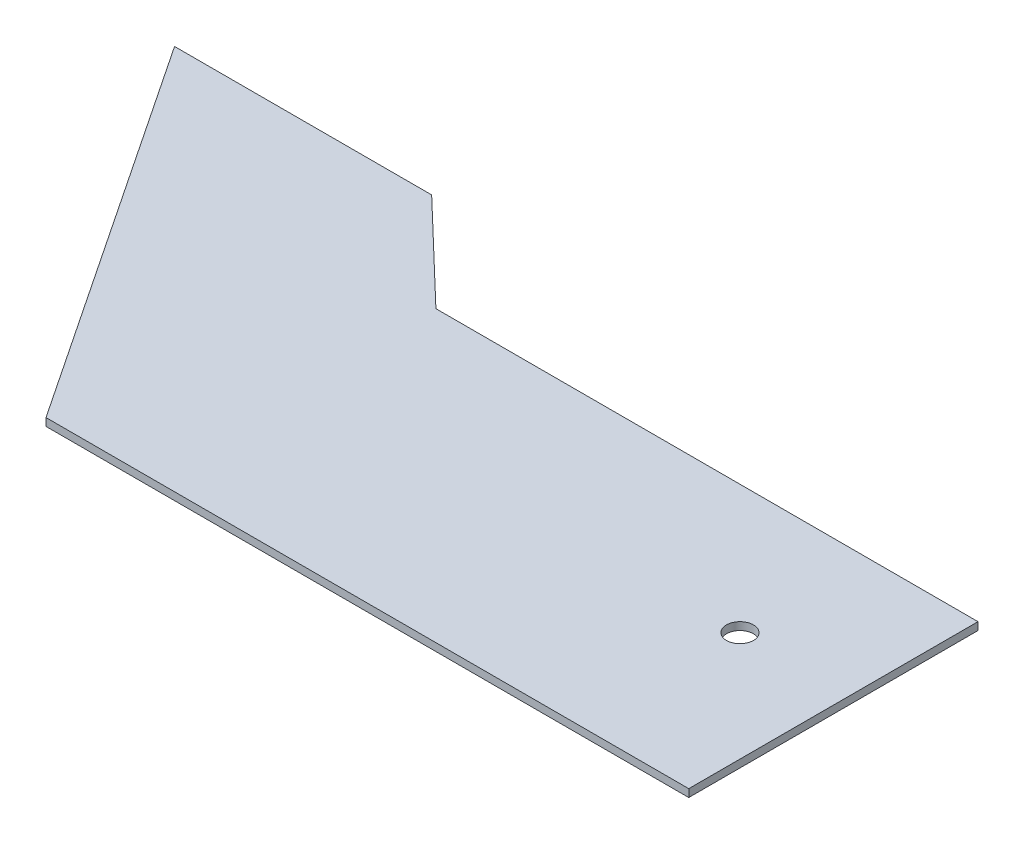
SolidWorks part; units mm, degrees
ref_plane "Front Plane" through (0, 0, 0) normal (0, 0, 1) x (1, 0, 0)
ref_plane "Top Plane" through (0, 0, 0) normal (0, 1, 0) x (1, 0, 0)
ref_plane "Right Plane" through (0, 0, 0) normal (1, 0, 0) x (0, 0, -1)
sketch "Sketch1" plane through (0, 0, 0) normal (0, 1, 0) x (1, 0, 0)
  line L0 (22.3813, 25.641) -> (56.4442, 25.6396) construction
  line L1 (-80.5873, 50.6403) -> (-45.5873, 0.6403)
  line L2 (-45.5873, 0.6403) -> (124.4127, 0.6403)
  line L4 (-80.5873, 50.6403) -> (159.4127, 50.6403)
  line L6 (-50.0418, 7.0039) -> (159.4127, 50.6403) construction
  line L7 (-80.5873, 50.6403) -> (128.8673, 7.0039) construction
  line L8 (159.4127, 50.6403) -> (124.4127, 0.6403)
  circle A0 centre (22.3813, 25.641) radius 2.1
  circle A1 centre (56.4442, 25.6396) radius 2.1
  point P4 (39.4127, 25.6403)
  dimension "D1" = 240
sketch "Sketch2" plane through (0, 0, 0) normal (0, 1, 0) x (1, 0, 0)
  line L0 (39.4127, 50.6403) -> (39.4127, 0.6403)
  line L1 (-80.5873, 50.6403) -> (159.4127, 50.6403) construction
  line L2 (-45.5873, 0.6403) -> (124.4127, 0.6403) construction
  line L3 (39.4127, 0.6403) -> (-45.5873, 0.6403)
  line L4 (-45.5873, 0.6403) -> (-80.5873, 50.6403)
  line L5 (-80.5873, 50.6403) -> (39.4127, 50.6403)
  circle A0 centre (22.3813, 25.641) radius 2.1
extrude "Boss-Extrude1" add sketch "Sketch2" along normal blind 1.2
sketch "Sketch3" plane through (0, 1.2, 0) normal (0, 1, 0) x (1, 0, 0)
  line L0 (39.4127, 40.6403) -> (-30.5873, 40.6403)
  line L1 (39.4127, 0.6403) -> (39.4127, 50.6403) construction
  line L2 (-30.5873, 40.6403) -> (-50.5873, 50.6403)
  line L3 (39.4127, 50.6403) -> (-80.5873, 50.6403) construction
  line L4 (-50.5873, 50.6403) -> (39.4127, 50.6403)
  line L5 (39.4127, 50.6403) -> (39.4127, 40.6403)
  dimension "D1" = 70
  dimension "D2" = 10
  dimension "D3" = 90
extrude "Cut-Extrude1" cut sketch "Sketch3" against normal blind 1.5
sketch "Sketch4" plane through (0, 1.2, 0) normal (0, 1, 0) x (1, 0, 0)
  line L1 (39.4127, 0.6403) -> (-60.5873, 0.6403)
  line L2 (39.4127, 0.6403) -> (39.4127, 45.6403)
  line L3 (-60.5873, 60.6403) -> (-100.5873, 60.6403)
  line L5 (39.4127, 45.6403) -> (-44.9268, 45.6403)
  line L6 (-44.9268, 45.6403) -> (-60.5873, 60.6403)
  line L7 (-100.5873, 60.6403) -> (-60.5873, 0.6403)
  circle A0 centre (22.3813, 25.641) radius 2.1
  dimension "D2" = 40
  dimension "D3" = 15
extrude "Boss-Extrude3" add sketch "Sketch4" against normal up to surface (1.2 mm away) contours L2 L5 L6 L3 L7 L1 | A0 up to face at (-21.4206, 0, -30.6403)
sketch "Sketch6" plane through (0, 1.2, 0) normal (0, 1, 0) x (1, 0, 0)
  line L0 (-49.666, 50.1797) -> (-44.9268, 45.6403)
  line L1 (-40.5873, 45.6403) -> (-44.9268, 45.6403)
  line L2 (-49.666, 50.1797) -> (-40.5873, 45.6403)
  line L3 (-49.666, 50.1797) -> (-44.9268, 45.6403)
  line M1 (-40.5873, 45.6403) -> (-49.666, 50.1797)
extrude "Cut-Extrude2" cut sketch "Sketch6" against normal blind 1.5 contours L1 L0 M1
sketch "Sketch7" plane through (0, 1.2, 0) normal (0, 1, 0) x (1, 0, 0)
  line L0 (39.4127, 0.6403) -> (-2.757, 45.6403)
  line L1 (39.4127, 45.6403) -> (-44.9268, 45.6403) construction
  line L2 (-2.757, 45.6403) -> (39.4127, 45.6403)
  line L3 (39.4127, 45.6403) -> (39.4127, 0.6403)
  line L4 (-2.757, 45.6403) -> (-2.757, 47.6403)
  line L5 (-2.757, 47.6403) -> (39.4127, 47.6403)
  line L6 (39.4127, 47.6403) -> (39.4127, 45.6403)
  circle A0 centre (22.3813, 25.641) radius 2.1
  dimension "D1" = 2
